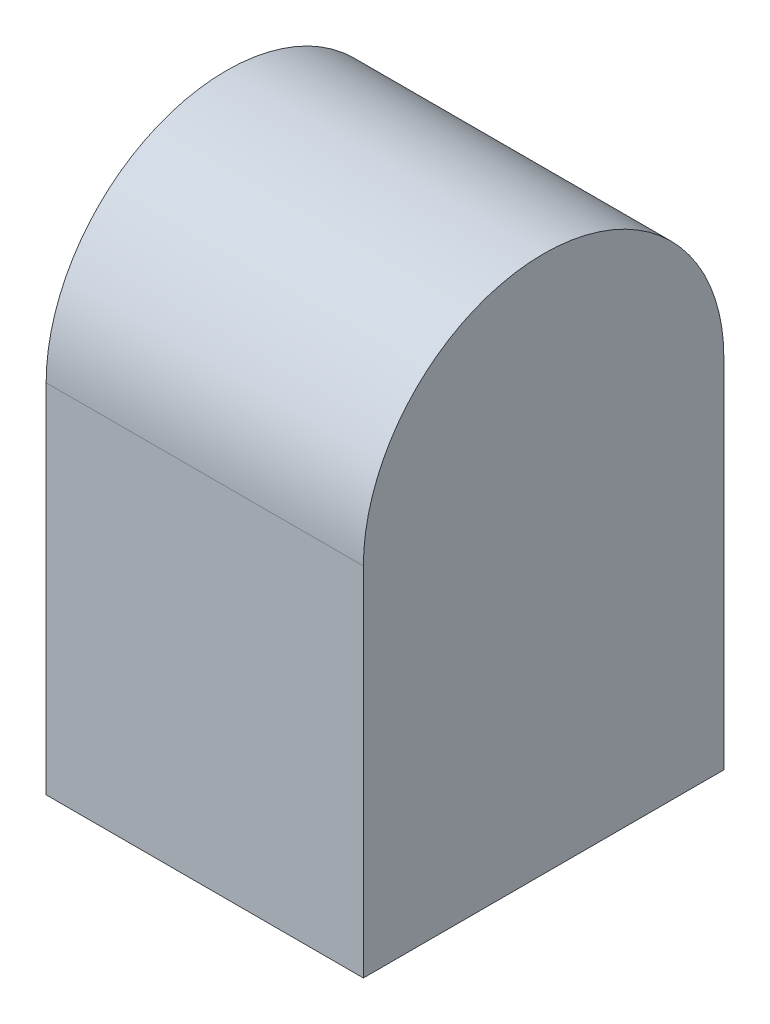
SolidWorks part; units mm, degrees
ref_plane "Front Plane" through (0, 0, 0) normal (0, 0, 1) x (1, 0, 0)
ref_plane "Top Plane" through (0, 0, 0) normal (0, 1, 0) x (1, 0, 0)
ref_plane "Right Plane" through (0, 0, 0) normal (1, 0, 0) x (0, 0, -1)
sketch "Sketch1" plane through (0, 0, 0) normal (0, 1, 0) x (1, 0, 0)
  line L1 (0, 0) -> (0.044, 0)
  line L2 (0, 0) -> (0, 0.05)
  line L3 (0, 0.05) -> (0.044, 0.05)
  line L4 (0.044, 0) -> (0.044, 0.05)
  dimension "D1" = 0.044
  dimension "D2" = 0.05
extrude "Boss-Extrude1" add sketch "Sketch1" along normal blind 0.0495
sketch "Sketch3" plane through (0, 0, 0) normal (-1, 0, 0) x (0, 0, 1)
  line L0 (-0.05, 0.0495) -> (0, 0.0495) construction
  circle A0 centre (-0.025, 0.0495) radius 0.025
  dimension "D1" = 0.05
extrude "Boss-Extrude2" add sketch "Sketch3" against normal blind 0.044
